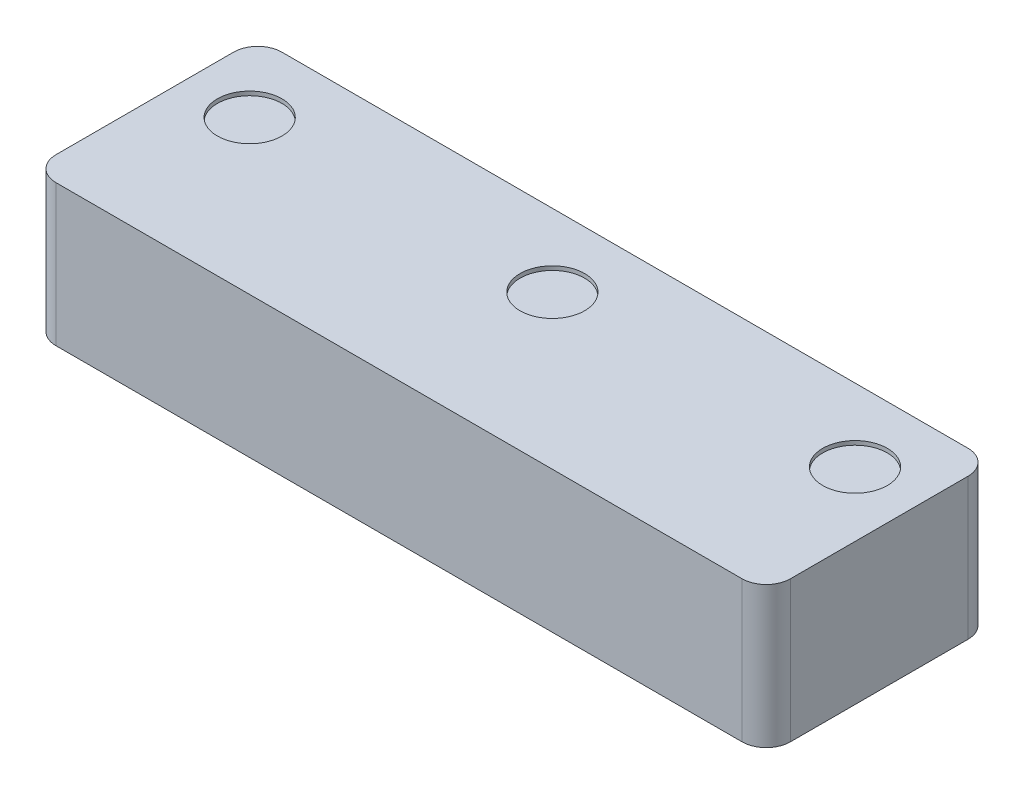
SolidWorks part; units mm, degrees
material "6061-T6 (SS)"
ref_plane "Front Plane" through (0, 0, 0) normal (0, 0, 1) x (1, 0, 0)
ref_plane "Top Plane" through (0, 0, 0) normal (0, 1, 0) x (1, 0, 0)
ref_plane "Right Plane" through (0, 0, 0) normal (1, 0, 0) x (0, 0, -1)
sketch "Sketch1" plane through (0, 0, 0) normal (0, 1, 0) x (1, 0, 0)
  line L1 (0, 0) -> (91, 0)
  line L2 (0, 0) -> (0, 28)
  line L3 (0, 28) -> (91, 28)
  line L4 (91, 0) -> (91, 28)
  dimension "D1" = 91
  dimension "D2" = 28
extrude "Boss-Extrude1" add sketch "Sketch1" along normal blind 17.5
sketch "Sketch2" plane through (0, 17.5, 0) normal (0, 1, 0) x (1, 0, 0)
  line L0 (8, 19) -> (83, 19) construction
  line L1 (8, 19) -> (0, 19) construction
  line L2 (0, 28) -> (0, 0) construction
  line L3 (83, 19) -> (91, 19) construction
  line L4 (91, 0) -> (91, 28) construction
  line L5 (8, 19) -> (8, 28) construction
  line L6 (91, 28) -> (0, 28) construction
  line L7 (0, 0) -> (91, 0) construction
  circle A0 centre (45.5, 19) radius 4
  circle A1 centre (8, 19) radius 4
  circle A2 centre (83, 19) radius 4
  dimension "D1" = 75
  dimension "D2" = 8
  dimension "D3" = 19
extrude "Cut-Extrude1" cut sketch "Sketch2" against normal blind 0.5
sketch "Sketch3" plane through (0, 0, 0) normal (0, -1, 0) x (1, 0, 0)
  line L0 (83, -18.5) -> (8, -18.5) construction
  line L1 (83, -18.5) -> (91, 0) construction
  line L2 (8, -18.5) -> (0, 0) construction
  line L3 (0, 0) -> (91, 0) construction
  circle A0 centre (83, -18.5) radius 2
  circle A1 centre (8, -18.5) radius 2
  dimension "D1" = 75
  dimension "D3" = 4
  dimension "D2" = 18.5
extrude "Cut-Extrude2" cut sketch "Sketch3" against normal blind 6.5
fillet "Fillet1" radius 3 4 edges at (0, 8.75, 0) (0, 8.75, -28) (91, 8.75, 0) (91, 8.75, -28)
